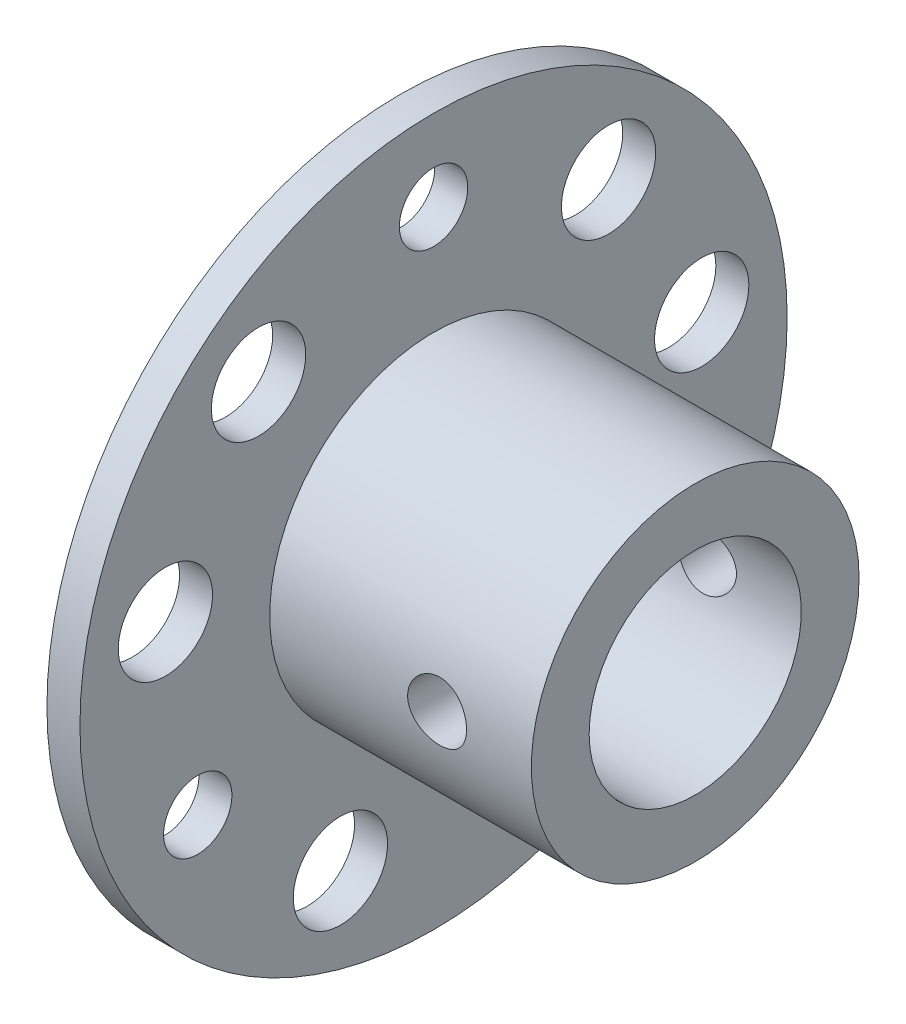
SolidWorks part; units mm, degrees
ref_plane "Front Plane" through (0, 0, 0) normal (0, 0, 1) x (1, 0, 0)
ref_plane "Top Plane" through (0, 0, 0) normal (0, 1, 0) x (1, 0, 0)
ref_plane "Right Plane" through (0, 0, 0) normal (1, 0, 0) x (0, 0, -1)
sketch "Sketch1" plane through (0, 0, 0) normal (0, 0, 1) x (1, 0, 0)
  line L0 (0, 15) -> (0, 0)
  line L1 (0, 0) -> (1.4, 0)
  line L2 (1.4, 0) -> (1.4, 15)
  line L3 (1.4, 15) -> (0, 15)
  line L4 (0, 0) -> (1.4, 0) construction
  dimension "D1" = 1.4
  dimension "D2" = 15
revolve "Revolve1" add sketch "Sketch1" angle 360 about L4
sketch "Sketch2" plane through (1.4, 0, 0) normal (1, 0, 0) x (0, 0, -1)
  circle A0 centre (0, 0) radius 6.95
extrude "Boss-Extrude1" add sketch "Sketch2" along normal blind 11.1
hole_wizard "Ø4.0 (4) Diameter Hole1" positions "Sketch4" profile "Sketch3" hole size "Ø4.0" standard "ANSI Metric"
sketch "Sketch4" plane through (1.4, 0, 0) normal (1, 0, 0) x (0, 0, -1)
  point P0 (-7.4242, 8.8478)
  point P1 (-11.3745, 2.0056)
  point P2 (-3.9503, -10.8534)
  point P3 (3.9503, -10.8534)
  point P4 (11.3745, 2.0056)
  point P5 (7.4242, 8.8478)
sketch "Sketch3" plane through (1.4, 8.8478, 7.4242) normal (0, 1, 0) x (0, 0, -1)
  line L0 (0, 0) -> (0, 1.4)
  line L1 (0, 1.4) -> (2, 1.4)
  line L2 (2, 1.4) -> (2, 0)
  line L5 (2, 0) -> (0, 0)
  line L11 (0, -6.35) -> (0, 107.95) construction
  dimension "Thru Hole Dia." = 4
  dimension "Thru Hole Depth" = 1.4
hole_wizard "Ø2.9 (2.9) Diameter Hole1" positions "Sketch6" profile "Sketch5" hole size "Ø2.9" standard "ANSI Metric"
sketch "Sketch6" plane through (1.4, 0, 0) normal (1, 0, 0) x (0, 0, -1)
  point P0 (0, 11.55)
  point P1 (-10.0026, -5.775)
  point P2 (10.0026, -5.775)
sketch "Sketch5" plane through (1.4, 11.55, 0) normal (0, 1, 0) x (0, 0, -1)
  line L0 (0, 0) -> (0, 1.4)
  line L1 (0, 1.4) -> (1.45, 1.4)
  line L2 (1.45, 1.4) -> (1.45, 0)
  line L5 (1.45, 0) -> (0, 0)
  line L11 (0, -6.35) -> (0, 107.95) construction
  dimension "Thru Hole Dia." = 2.9
  dimension "Thru Hole Depth" = 1.4
hole_wizard "Ø9.0 (9) Diameter Hole1" positions "Sketch8" profile "Sketch7" hole size "Ø9.0" standard "ANSI Metric"
sketch "Sketch8" plane through (0, 0, 0) normal (-1, 0, 0) x (0, 0, 1)
  point P0 (0, 0)
sketch "Sketch7" plane through (0, 0, 0) normal (0, 1, 0) x (0, 0, 1)
  line L0 (0, 0) -> (0, 12.5)
  line L1 (0, 12.5) -> (4.5, 12.5)
  line L2 (4.5, 12.5) -> (4.5, 0)
  line L5 (4.5, 0) -> (0, 0)
  line L11 (0, -6.35) -> (0, 107.95) construction
  dimension "Thru Hole Dia." = 9
  dimension "Thru Hole Depth" = 12.5
ref_plane "Plane1" through (0, 0, -4.3229) normal (0, 0, 1) x (1, 0, 0)
hole_wizard "Ø2.5 (2.5) Diameter Hole1" positions "Sketch10" profile "Sketch9" hole size "Ø2.5" standard "ANSI Metric"
sketch "Sketch10" plane through (0, 0, -4.3229) normal (0, 0, 1) x (1, 0, 0)
  point P0 (8.5, 0)
sketch "Sketch9" plane through (8.5, 0, -4.3229) normal (1, 0, 0) x (0, -1, 0)
  line L0 (0, 0) -> (0, 10.6771)
  line L1 (0, 10.6771) -> (1.25, 10.6771)
  line L2 (1.25, 10.6771) -> (1.25, 0)
  line L5 (1.25, 0) -> (0, 0)
  line L11 (0, -6.35) -> (0, 107.95) construction
  dimension "Thru Hole Dia." = 2.5
  dimension "Thru Hole Depth" = 10.6771
ref_plane "Plane2" through (0, 0, 4.3229) normal (0, 0, -1) x (-1, 0, 0)
hole_wizard "Ø2.5 (2.5) Diameter Hole2" positions "Sketch12" profile "Sketch11" hole size "Ø2.5" standard "ANSI Metric"
sketch "Sketch12" plane through (0, 0, 4.3229) normal (0, 0, -1) x (-1, 0, 0)
  point P0 (-8.5, 0)
sketch "Sketch11" plane through (8.5, 0, 4.3229) normal (1, 0, 0) x (0, 1, 0)
  line L0 (0, 0) -> (0, 10.6771)
  line L1 (0, 10.6771) -> (1.25, 10.6771)
  line L2 (1.25, 10.6771) -> (1.25, 0)
  line L5 (1.25, 0) -> (0, 0)
  line L11 (0, -6.35) -> (0, 107.95) construction
  dimension "Thru Hole Dia." = 2.5
  dimension "Thru Hole Depth" = 10.6771
